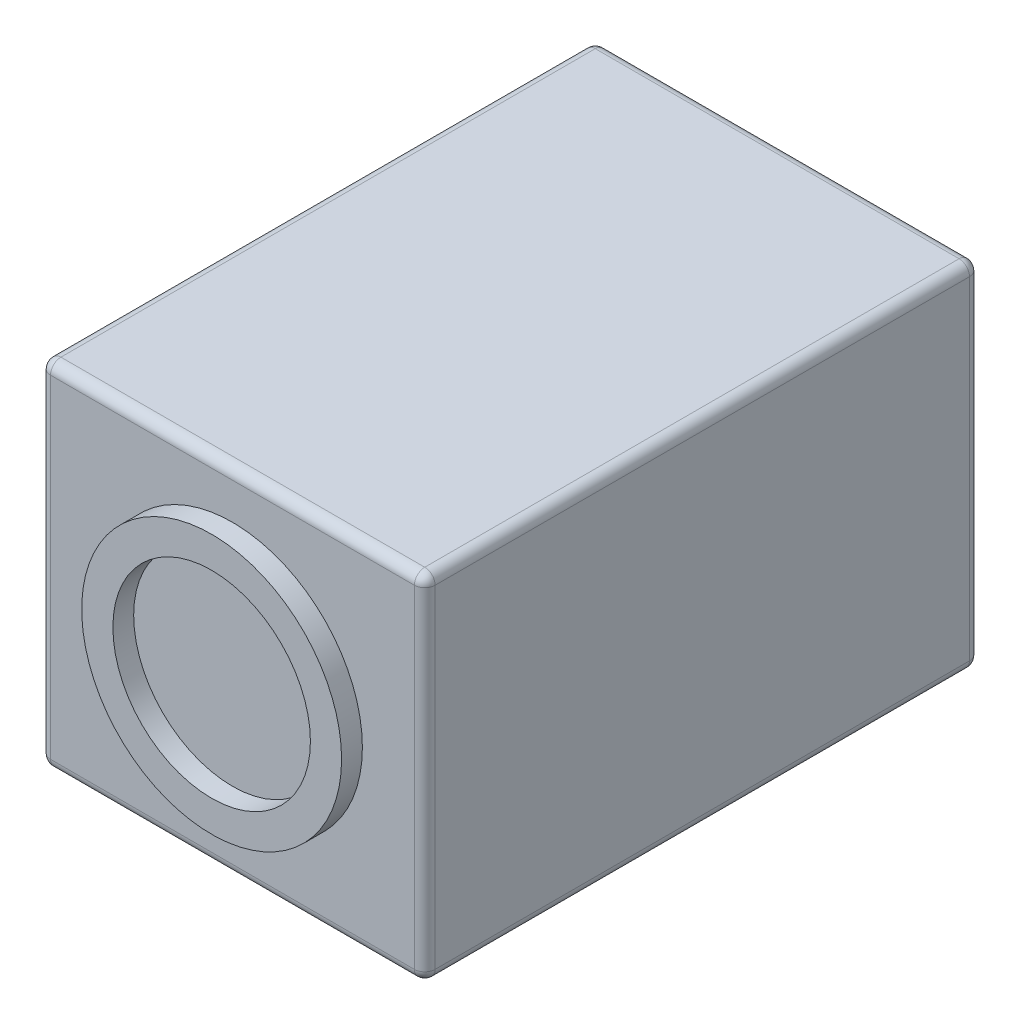
SolidWorks part; units mm, degrees
material "1060 Alloy"
ref_plane "Front Plane" through (0, 0, 0) normal (0, 0, 1) x (1, 0, 0)
ref_plane "Top Plane" through (0, 0, 0) normal (0, 1, 0) x (1, 0, 0)
ref_plane "Right Plane" through (0, 0, 0) normal (1, 0, 0) x (0, 0, -1)
sketch "Sketch1" plane through (0, 0, 0) normal (0, 0, 1) x (1, 0, 0)
  line L1 (-23.495, 21.59) -> (23.495, 21.59)
  line L2 (-23.495, 21.59) -> (-23.495, -21.59)
  line L3 (-23.495, -21.59) -> (23.495, -21.59)
  line L4 (23.495, 21.59) -> (23.495, -21.59)
  dimension "D1" = 46.99
  dimension "D2" = 43.18
  dimension "D3" = 23.495
  dimension "D4" = 21.59
extrude "Extrude1" add sketch "Sketch1" along normal blind 67.818
fillet "Fillet2" radius 1.27 12 edges at (0, -21.59, 0) (0, -21.59, 67.818) (23.495, -21.59, 33.909) (23.495, 0, 67.818) (23.495, 0, 0) (-23.495, 0, 67.818) (-23.495, 0, 0) (23.495, 21.59, 33.909) (0, 21.59, 67.818) (-23.495, 21.59, 33.909) (0, 21.59, 0) (-23.495, -21.59, 33.909)
sketch "Sketch2" plane through (0, 0, 67.818) normal (0, 0, 1) x (1, 0, 0)
  circle A0 centre (0, 0) radius 15.875
  circle A1 centre (0, 0) radius 12.065
extrude "Extrude2" add sketch "Sketch2" along normal blind 2.54
sketch "Sketch3" plane through (0, -21.59, 0) normal (0, -1, 0) x (1, 0, 0)
  line L0 (-22.225, 67.818) -> (22.225, 67.818) construction
  line L1 (22.225, 1.27) -> (22.225, 66.548) construction
  line L2 (-22.225, 66.548) -> (-22.225, 1.27) construction
  circle A0 centre (-10.922, 39.1795) radius 1.0795
  circle A1 centre (10.795, 39.1795) radius 1.0795
  dimension "D1" = 28.6385
  dimension "D2" = 21.717
  dimension "D3" = 11.43
  dimension "D4" = 11.303
extrude "Cut-Extrude1" cut sketch "Sketch3" against normal blind 2.54
